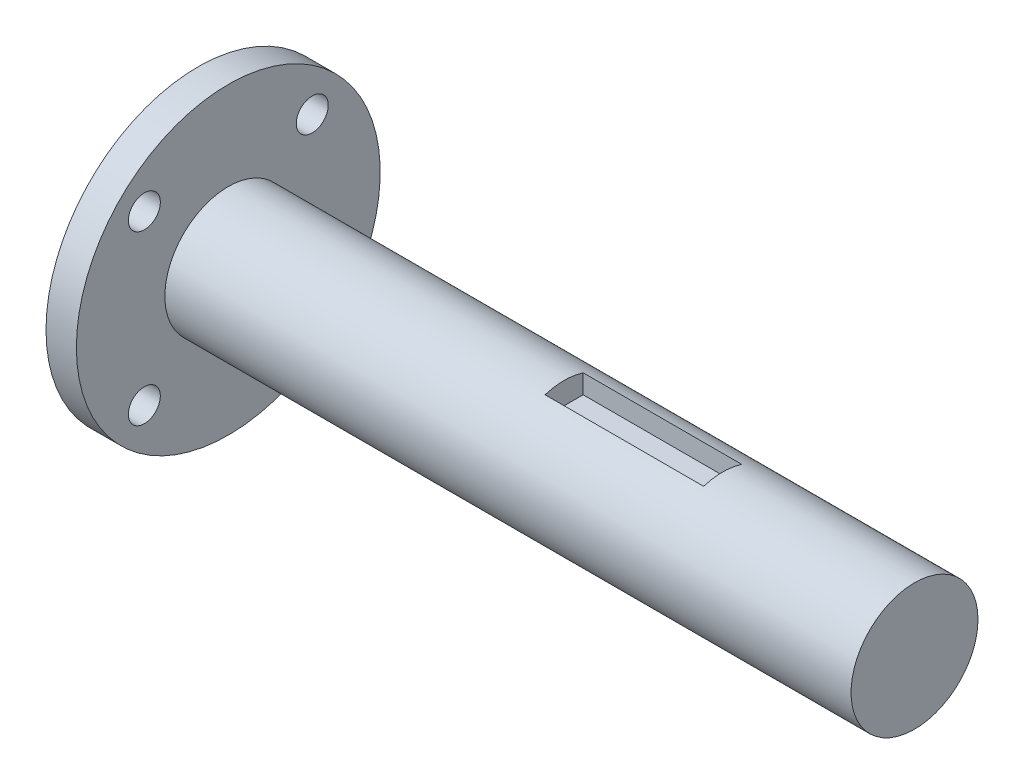
SolidWorks part; units mm, degrees
ref_plane "Piano frontale" through (0, 0, 0) normal (0, 0, 1) x (1, 0, 0)
ref_plane "Piano superiore" through (0, 0, 0) normal (0, 1, 0) x (1, 0, 0)
ref_plane "Piano destro" through (0, 0, 0) normal (1, 0, 0) x (0, 0, -1)
sketch "Sketch1" plane through (0, 0, 0) normal (1, 0, 0) x (0, 0, -1)
  circle A3 centre (0, 0) radius 7.9375
  dimension "D1" = 15.875
extrude "Boss-Extrude1" add sketch "Sketch1" along normal blind 42
sketch "Sketch4" plane through (0, 0, 0) normal (-1, 0, 0) x (0, 0, 1)
  line L0 (0, 10.5) -> (0, -10.5) construction
  line L1 (-10.5, 10.5) -> (10.5, 10.5) construction
  line L2 (-10.5, 10.5) -> (-10.5, -10.5) construction
  line L3 (-10.5, -10.5) -> (10.5, -10.5) construction
  line L4 (10.5, 10.5) -> (10.5, -10.5) construction
  line L5 (-10.5, 0) -> (10.5, 0) construction
  circle A0 centre (0, 0) radius 19
  circle A1 centre (0, 0) radius 10.75 construction
  circle A4 centre (-10.5, 10.5) radius 2
  circle A5 centre (10.5, 10.5) radius 2
  circle A6 centre (10.5, -10.5) radius 2
  circle A7 centre (-10.5, -10.5) radius 2
  point P23 (0, -10.5)
  point P31 (0, 0)
  dimension "D1" = 38
  dimension "D2" = 4
  dimension "D3" = 21
  dimension "21" = 21
extrude "Boss-Extrude3" add sketch "Sketch4" along normal blind 3.8
sketch "Sketch6" plane through (42, 0, 0) normal (1, 0, 0) x (0, 0, -1)
  line L1 (-2.3815, 5.1888) -> (2.3815, 5.1888)
  line L2 (-2.3815, 5.1888) -> (-2.3815, 7.5718)
  line L4 (2.3815, 5.1888) -> (2.3815, 7.5718)
  arc A0 (-2.3815, 7.5718) -> (2.3815, 7.5718) centre (0, 0) ccw
  point P7 (0, 5.1888)
  dimension "D3" = 15.875
  dimension "D1" = 2.383
  dimension "D2" = 4.763
extrude "Boss-Extrude5" add sketch "Sketch6" along normal blind 19.8272
sketch "Sketch7" plane through (61.8272, 0, 0) normal (1, 0, 0) x (0, 0, -1)
  circle A0 centre (0, 0) radius 7.9375
  dimension "D1" = 15.875
extrude "Boss-Extrude6" add sketch "Sketch7" along normal blind 24
